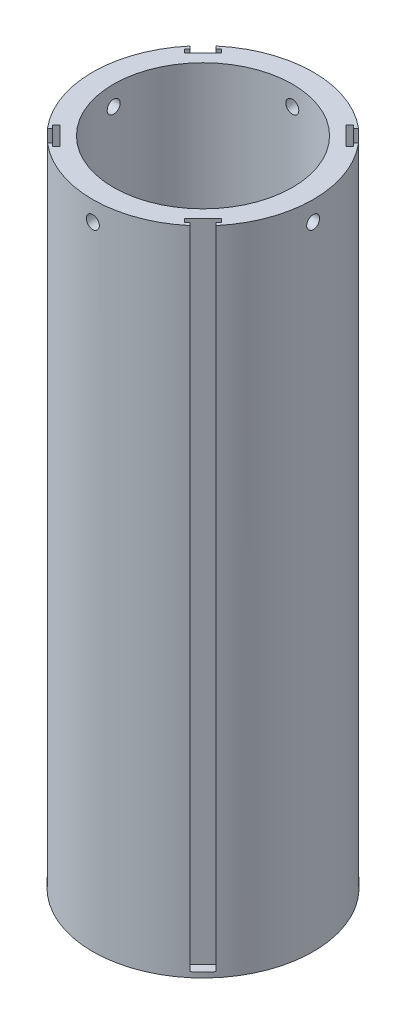
SolidWorks part; units mm, degrees
ref_plane "Front Plane" through (0, 0, 0) normal (0, 0, 1) x (1, 0, 0)
ref_plane "Top Plane" through (0, 0, 0) normal (0, 1, 0) x (1, 0, 0)
ref_plane "Right Plane" through (0, 0, 0) normal (1, 0, 0) x (0, 0, -1)
sketch "Sketch1" plane through (0, 0, 0) normal (0, 1, 0) x (1, 0, 0)
  line L0 (-14.125, -14.125) -> (-14.125, 0) construction
  line L1 (-14.125, 14.125) -> (-14.125, 0) construction
  line L2 (14.125, 14.125) -> (0, 14.125) construction
  line L3 (-14.125, 14.125) -> (0, 14.125) construction
  line L4 (14.125, 14.125) -> (14.125, 0) construction
  line L5 (14.125, 0) -> (14.125, -14.125) construction
  line L6 (14.125, -14.125) -> (0, -14.125) construction
  line L7 (0, -14.125) -> (-14.125, -14.125) construction
  line L8 (-14.125, -14.125) -> (14.125, 14.125) construction
  line L9 (-14.125, 14.125) -> (14.125, -14.125) construction
  line L10 (14.125, 14.125) -> (24.1129, 24.1129) construction
  line L11 (24.1129, 24.1129) -> (24.2897, 24.2897) construction
  circle A0 centre (0, 0) radius 34.3508
  circle A1 centre (0, 0) radius 42.3508
  circle A2 centre (-14.125, 14.125) radius 14.125 construction
  circle A3 centre (14.125, 14.125) radius 14.125 construction
  circle A4 centre (14.125, -14.125) radius 14.125 construction
  circle A5 centre (-14.125, -14.125) radius 14.125 construction
  point P17 (0, 0)
  dimension "D1" = 8
  dimension "D2" = 9.9879
  dimension "D3" = 28.25
  dimension "D4" = 28.25
  dimension "D5" = 28.25
  dimension "D6" = 28.25
  dimension "D7" = 68.7015
extrude "Boss-Extrude1" add sketch "Sketch1" along normal blind 250
sketch "Sketch2" plane through (0, 0, 0) normal (1, 0, 0) x (0, 0, -1)
  line L0 (42.3508, 250) -> (-42.3508, 250) construction
  circle A0 centre (0, 242.5) radius 2.5
  dimension "D2" = 5
  dimension "D1" = 7.5
extrude "Cut-Extrude1" cut sketch "Sketch2" against normal through all both and the other way through all
sketch "Sketch3" plane through (0, 0, 0) normal (0, 0, 1) x (1, 0, 0)
  line L0 (42.3508, 250) -> (-42.3508, 250) construction
  circle A0 centre (0, 242.5) radius 2.5
  dimension "D2" = 5
  dimension "D1" = 7.5
extrude "Cut-Extrude2" cut sketch "Sketch3" against normal through all both and the other way through all
ref_plane "Plane1" through (0, 2, 0) normal (0, -1, 0) x (-1, 0, 0)
sketch "Sketch4" plane through (0, 2, 0) normal (0, 1, 0) x (1, 0, 0)
  line L0 (-42.3508, 0) -> (42.3508, 0) construction
  line L1 (0, 0) -> (29.9465, 29.9465) construction
  line L2 (31.0072, 23.9361) -> (23.9361, 31.0072)
  line L6 (23.9361, 31.0072) -> (25.3503, 32.4214)
  line L7 (25.3503, 32.4214) -> (26.411, 31.3607)
  line L8 (26.411, 31.3607) -> (27.3692, 32.3189)
  line L9 (31.0072, 23.9361) -> (32.4214, 25.3503)
  line L10 (32.4214, 25.3503) -> (31.3607, 26.411)
  line L11 (31.3607, 26.411) -> (32.3189, 27.3692)
  circle A0 centre (0, 0) radius 42.3508 construction
  arc A3 (32.3189, 27.3692) -> (27.3692, 32.3189) centre (0, 0) ccw
  point P7 (0, 0)
  point P11 (0, 0)
  point P14 (0, 0)
  point P17 (27.4716, 27.4716)
  dimension "D4" = 2
  dimension "D1" = 45
  dimension "D2" = 3.5
  dimension "D3" = 2
  dimension "D5" = 1.5
  dimension "D6" = 1.5
  dimension "D7" = 10
  dimension "D8" = 1.4142
extrude "Cut-Extrude3" cut sketch "Sketch4" along normal through all
pattern_circular "CirPattern1" count 4 over 360 about axis through (0, 0, 0) along (0, 1, 0) of "Cut-Extrude3"
sketch "Sketch6" plane through (0, 0, 0) normal (0, 1, 0) x (1, 0, 0)
  line L0 (-13.2818, 13.2818) -> (-13.2818, -13.2818) construction
  line L1 (-13.2818, 13.2818) -> (13.2818, 13.2818) construction
  line L2 (-13.2818, 13.2818) -> (-21.7671, 21.7671) construction
  line L3 (-21.7671, 21.7671) -> (-24.2897, 24.2897) construction
  circle A0 centre (-13.2818, 13.2818) radius 12 construction
  circle A1 centre (-13.2818, -13.2818) radius 12 construction
  circle A2 centre (13.2818, 13.2818) radius 12 construction
  circle A3 centre (13.2818, -13.2818) radius 12 construction
  circle A4 centre (0, 0) radius 34.3508 construction
  circle A5 centre (0, 0) radius 34.3508
  circle A6 centre (-13.2818, 13.2818) radius 12.25
  circle A7 centre (13.2818, 13.2818) radius 12.25
  circle A8 centre (13.2818, -13.2818) radius 12.25
  circle A9 centre (-13.2818, -13.2818) radius 12.25
  point P8 (0, 13.2818)
  point P9 (-13.2818, 0)
  dimension "D1" = 24
  dimension "D2" = 24
  dimension "D3" = 24
  dimension "D4" = 24
  dimension "D8" = 24.5
  dimension "D9" = 24.5
  dimension "D10" = 24.5
  dimension "D11" = 24.5
  dimension "D5" = 45
  dimension "D7" = 26.5636
extrude "Boss-Extrude3" add sketch "Sketch6" along normal blind 10
sketch "Sketch8" plane through (0, 10, 0) normal (0, 1, 0) x (1, 0, 0)
  line L0 (0, -13.2818) -> (0, 0) construction
  line L1 (-13.2818, 0) -> (-13.2818, -1.0318) construction
  circle A0 centre (-13.2818, -13.2818) radius 12.25 construction
  circle A1 centre (0, 0) radius 34.3508
  circle A2 centre (0, 0) radius 34.3508 construction
  circle A3 centre (13.2818, -13.2818) radius 12.25 construction
  circle A4 centre (13.2818, 13.2818) radius 12.25 construction
  circle A5 centre (-13.2818, 13.2818) radius 12.25 construction
  circle A6 centre (-13.2818, -13.2818) radius 12.25
  circle A7 centre (13.2818, -13.2818) radius 12.25
  circle A8 centre (13.2818, 13.2818) radius 12.25
  circle A9 centre (-13.2818, 13.2818) radius 12.25
  arc A19 (0, 13.2818) -> (-13.2818, 0) centre (-13.2818, 13.2818) ccw
  arc A20 (13.2818, 0) -> (0, 13.2818) centre (13.2818, 13.2818) ccw
  arc A21 (0, -13.2818) -> (13.2818, 0) centre (13.2818, -13.2818) ccw
  arc A22 (-13.2818, 0) -> (0, -13.2818) centre (-13.2818, -13.2818) ccw
  dimension "D1" = 0
extrude "Boss-Extrude6" add sketch "Sketch8" along normal blind 90 contours A19 A22 A21 A20
sketch "Sketch9" plane through (0, 100, 0) normal (0, 1, 0) x (1, 0, 0)
  circle A0 centre (0, 0) radius 34.3508 construction
  circle A1 centre (0, 0) radius 34.3508
  circle A2 centre (-13.2818, -13.2818) radius 12.25 construction
  circle A3 centre (13.2818, -13.2818) radius 12.25 construction
  circle A4 centre (13.2818, 13.2818) radius 12.25 construction
  circle A5 centre (-13.2818, 13.2818) radius 12.25 construction
  circle A6 centre (-13.2818, -13.2818) radius 12.25 construction
  circle A7 centre (13.2818, -13.2818) radius 12.25 construction
  circle A8 centre (13.2818, 13.2818) radius 12.25 construction
  circle A9 centre (-13.2818, 13.2818) radius 12.25 construction
  circle A10 centre (-13.2818, 13.2818) radius 9.75
  circle A11 centre (13.2818, 13.2818) radius 9.75
  circle A12 centre (13.2818, -13.2818) radius 9.75
  circle A13 centre (-13.2818, -13.2818) radius 9.75
  dimension "D1" = 2.5
  dimension "D2" = 2.5
  dimension "D3" = 2.5
  dimension "D4" = 2.5
extrude "Boss-Extrude7" add sketch "Sketch9" along normal blind 10
